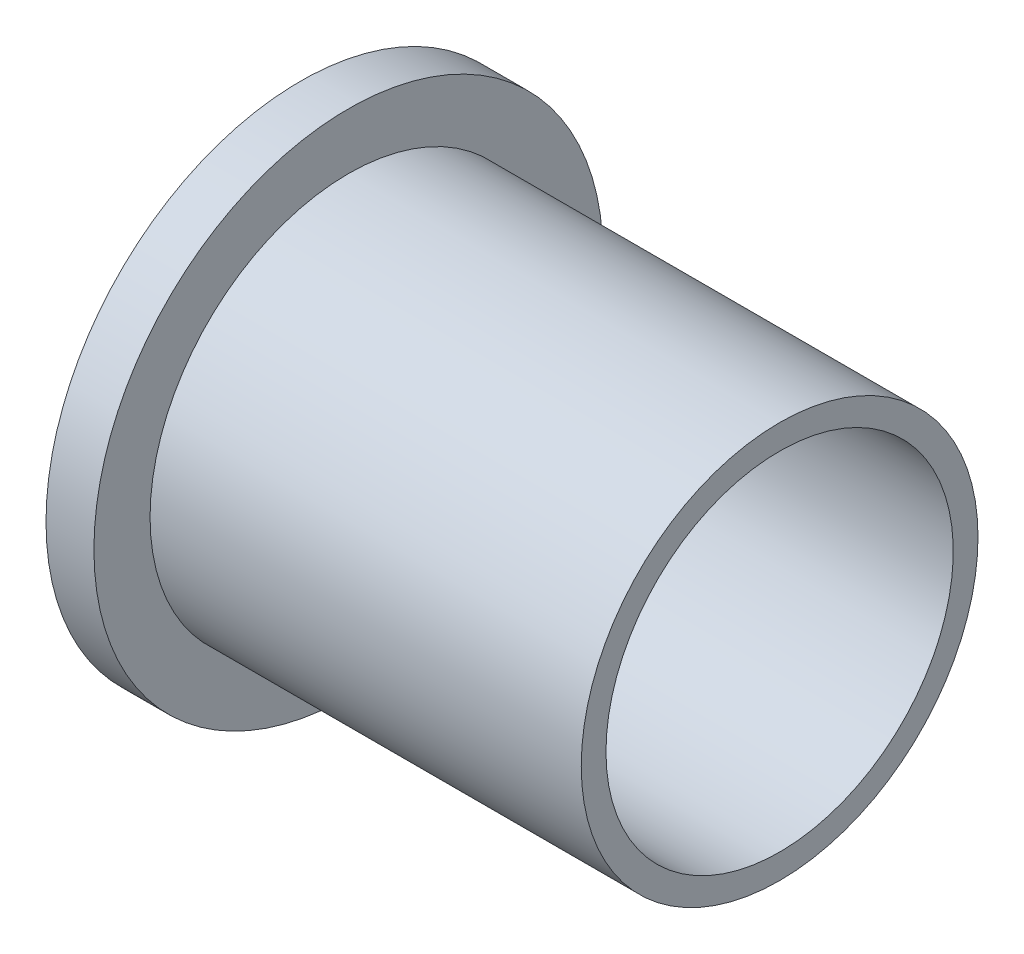
SolidWorks part; units mm, degrees
material "PE High Density"
ref_plane "Front Plane" through (0, 0, 0) normal (0, 0, 1) x (1, 0, 0)
ref_plane "Top Plane" through (0, 0, 0) normal (0, 1, 0) x (1, 0, 0)
ref_plane "Right Plane" through (0, 0, 0) normal (1, 0, 0) x (0, 0, -1)
sketch "Crossection" plane through (0, 0, 0) normal (0, 0, 1) x (1, 0, 0)
  line L0 (0, 0) -> (59.4575, 0) construction
  line L1 (0, 107.95) -> (0, 73.6473)
  line L2 (0, 73.6473) -> (203.2, 73.6473)
  line L3 (203.2, 73.6473) -> (203.2, 84.1375)
  line L4 (203.2, 84.1375) -> (20.32, 84.1375)
  line L5 (20.32, 84.1375) -> (20.32, 107.95)
  line L6 (20.32, 107.95) -> (0, 107.95)
  dimension "D1" = 73.6473
  dimension "D2" = 84.1375
  dimension "D3" = 20.32
  dimension "D4" = 203.2
  dimension "D5" = 107.95
revolve "Revolve" add sketch "Crossection" angle 360 about L0
equation "\"ID\"= 5.799in'EPG"
equation "\"OD\"= 6.625in'EPG"
equation "\"A\"= 8in'EPG"
equation "\"T\"= 0.8in'EPG"
equation "\"C\"= 8.5in'EPG"
equation "\"D1@Crossection\" = \"ID\" / 2"
equation "\"D2@Crossection\" = \"OD\" / 2"
equation "\"D3@Crossection\" = \"T\""
equation "\"D4@Crossection\" = \"A\""
equation "\"D5@Crossection\" = \"C\" / 2"
